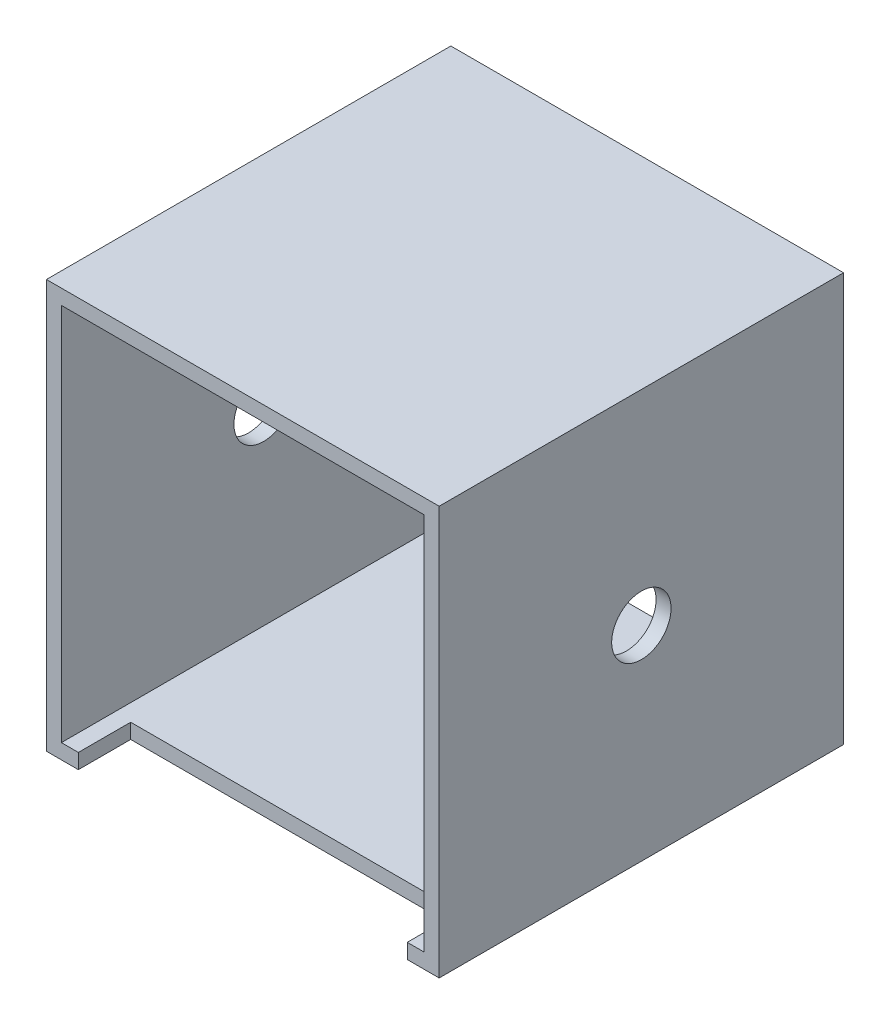
SolidWorks part; units mm, degrees
ref_plane "Front Plane" through (0, 0, 0) normal (0, 0, 1) x (1, 0, 0)
ref_plane "Top Plane" through (0, 0, 0) normal (0, 1, 0) x (1, 0, 0)
ref_plane "Right Plane" through (0, 0, 0) normal (1, 0, 0) x (0, 0, -1)
sketch "Sketch1" plane through (0, 0, 0) normal (0, 0, 1) x (1, 0, 0)
  line L1 (-33.3629, -34.7091) -> (33.3629, -34.7091)
  line L2 (-33.3629, -34.7091) -> (-33.3629, 34.7091)
  line L3 (-33.3629, 34.7091) -> (33.3629, 34.7091)
  line L4 (33.3629, -34.7091) -> (33.3629, 34.7091)
  line L5 (-33.3629, -34.7091) -> (33.3629, 34.7091) construction
  line L6 (-33.3629, 34.7091) -> (33.3629, -34.7091) construction
  point P0 (0, 0)
  dimension "D1" = 69.4182
  dimension "D2" = 66.7258
extrude "Extrude-Thin1" add sketch "Sketch1" along normal blind 68.707 thin thin type one direction reverse wall 2.54
hole_wizard "3/8 Clearance Hole1" positions "Sketch2" profile "Sketch3" hole size "3/8" standard "ANSI Inch" end condition through all
sketch "Sketch2" plane through (33.3629, 0, 0) normal (1, 0, 0) x (0, 0, -1)
  line L0 (-68.707, 34.7091) -> (0, 34.7091) construction
  point P0 (-34.3535, 0)
  point P4 (0, 0)
  point P7 (-34.3535, 34.7091)
sketch "Sketch3" plane through (33.3629, 0, 34.3535) normal (0, 1, 0) x (0, 0, -1)
  line L0 (0, 0) -> (0, 66.7258)
  line L1 (0, 66.7258) -> (5.0419, 66.7258)
  line L2 (5.0419, 66.7258) -> (5.0419, 0)
  line L5 (5.0419, 0) -> (0, 0)
  line L11 (0, -6.35) -> (0, 107.95) construction
  dimension "Thru Hole Dia." = 10.0838
  dimension "Thru Hole Depth" = 66.7258
sketch "Sketch4" plane through (0, -32.1691, 0) normal (0, 1, 0) x (1, 0, 0)
  line L1 (-27.94, -68.707) -> (27.94, -68.707)
  line L2 (-27.94, -68.707) -> (-27.94, -59.817)
  line L3 (-27.94, -59.817) -> (27.94, -59.817)
  line L4 (27.94, -68.707) -> (27.94, -59.817)
  line L5 (-30.8229, -68.707) -> (30.8229, -68.707) construction
  point P4 (-24.2341, -67.0477)
  point P6 (-23.5147, -68.707)
  point P8 (0, -68.707)
  point P9 (0, -59.817)
  dimension "D1" = 8.89
  dimension "D2" = 55.88
extrude "Cut-Extrude1" cut sketch "Sketch4" against normal through all
